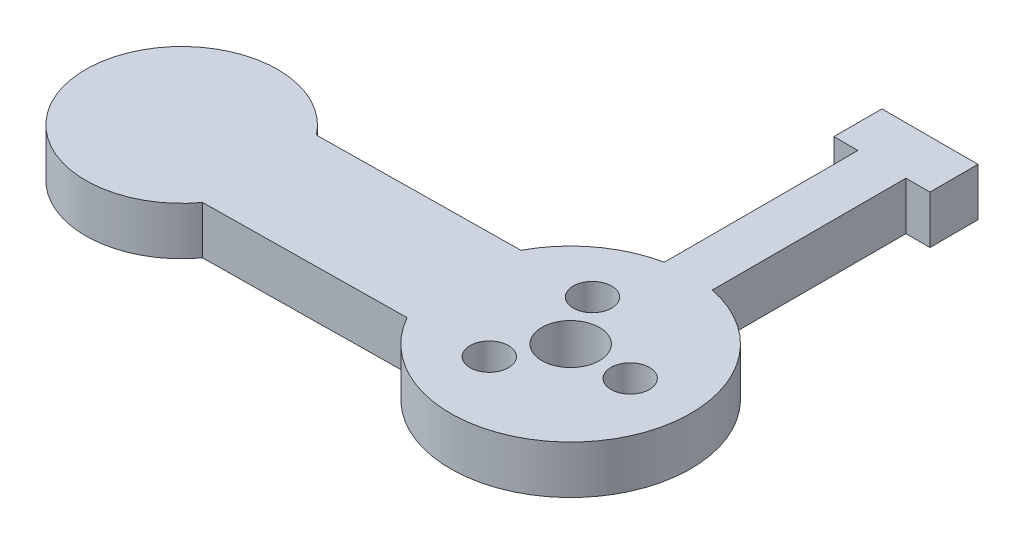
SolidWorks part; units mm, degrees
ref_plane "Front Plane" through (0, 0, 0) normal (0, 0, 1) x (1, 0, 0)
ref_plane "Top Plane" through (0, 0, 0) normal (0, 1, 0) x (1, 0, 0)
ref_plane "Right Plane" through (0, 0, 0) normal (1, 0, 0) x (0, 0, -1)
sketch "Sketch1" plane through (0, 0, 0) normal (0, 1, 0) x (1, 0, 0)
  line L0 (-55, 0) -> (55, 0) construction
  line L1 (0, 0) -> (-39.997, -0.4887) construction
  line L2 (0, 0) -> (0, 32.4) construction
  line L3 (0, -55) -> (0, 55) construction
  line L4 (-17.8975, 32.4) -> (19.2485, 32.4) construction
  line L5 (-10.8917, -6.1335) -> (-31.9243, -6.3905)
  line L6 (2.5, 12.2474) -> (-2.5, 12.2474)
  line L7 (2.5, 12.2474) -> (2.5, 32.4)
  line L8 (2.5, 32.4) -> (-2.5, 32.4)
  line L9 (-2.5, 12.2474) -> (-2.5, 32.4)
  line L10 (-11.0383, 5.8656) -> (-32.0709, 5.6086)
  line L12 (-5, 37.4) -> (5, 37.4)
  line L13 (-5, 37.4) -> (-5, 32.4)
  line L14 (-5, 32.4) -> (5, 32.4)
  line L15 (5, 37.4) -> (5, 32.4)
  line L16 (-5, 37.4) -> (5, 32.4) construction
  line L17 (-5, 32.4) -> (5, 37.4) construction
  circle A0 centre (0, 0) radius 12.5
  circle A1 centre (0, 0) radius 3
  circle A2 centre (6.2, 0) radius 2
  circle A5 centre (-39.997, -0.4887) radius 10
  circle A6 centre (-3.1, -5.3694) radius 2
  circle A7 centre (-3.1, 5.3694) radius 2
  point P14 (0, 0)
  point P28 (0, 34.9)
  point P36 (0, 0)
  dimension "D1" = 25
  dimension "D2" = 6
  dimension "D3" = 4
  dimension "D7" = 20
  dimension "D4" = 6.2
  dimension "D5" = 0.7
  dimension "D6" = 40
  dimension "D8" = 32.4
  dimension "D9" = 5
  dimension "D10" = 6
  dimension "D11" = 5
  dimension "D12" = 10
  dimension "D13" = 3
extrude "Boss-Extrude1" add sketch "Sketch1" along normal blind 5
